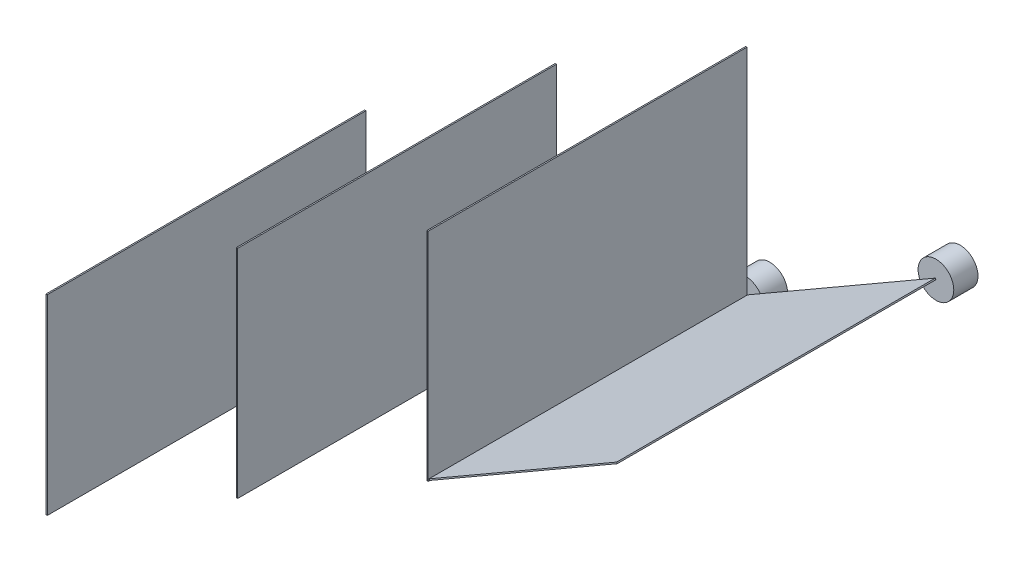
SolidWorks part; units mm, degrees
ref_plane "前视基准面" through (0, 0, 0) normal (0, 0, 1) x (1, 0, 0)
ref_plane "上视基准面" through (0, 0, 0) normal (0, 1, 0) x (1, 0, 0)
ref_plane "右视基准面" through (0, 0, 0) normal (1, 0, 0) x (0, 0, -1)
other "Configuration Table"
sketch "草图1" plane through (0, 0, 0) normal (0, 0, 1) x (1, 0, 0)
  line L0 (0, 0) -> (47.6566, 0) construction
  line L1 (0, 0) -> (147.2243, 85)
  line L2 (0, 0) -> (-0.5, 0.866)
  line L3 (147.2243, 85) -> (146.7243, 85.866)
  line L4 (-0.5, 0.866) -> (146.7243, 85.866)
  line L5 (-2.1651, -1.25) -> (0, 0) construction
  line L6 (-2.1651, -1.25) -> (-151.5544, -87.5) construction
  line L7 (-1.1651, -1.25) -> (-2.1651, -1.25)
  line L8 (-1.1651, -1.25) -> (-1.1651, 168.75)
  line L9 (-1.1651, 168.75) -> (-2.1651, 168.75)
  line L10 (-2.1651, -1.25) -> (-2.1651, 168.75)
  line L11 (-151.5544, -87.5) -> (-300.9438, -173.75) construction
  line L12 (-151.5544, -87.5) -> (-150.5544, -87.5)
  line L13 (-151.5544, -87.5) -> (-151.5544, 82.5)
  line L14 (-151.5544, 82.5) -> (-150.5544, 82.5)
  line L15 (-150.5544, -87.5) -> (-150.5544, 82.5)
  line L17 (-300.9438, -173.75) -> (-299.9438, -173.75)
  line L18 (-300.9438, -173.75) -> (-300.9438, -23.75)
  line L19 (-300.9438, -23.75) -> (-299.9438, -23.75)
  line L20 (-299.9438, -173.75) -> (-299.9438, -23.75)
  dimension "D1" = 30
sketch "草图2" plane through (0, 0, 0) normal (0, 0, 1) x (1, 0, 0)
  circle A0 centre (147.2243, 85) radius 14
  circle A1 centre (-2.1651, -1.25) radius 14
  circle A2 centre (-151.5544, -87.5) radius 14
  circle A3 centre (-300.9438, -173.75) radius 14
extrude "凸台-拉伸2" add sketch "草图1" along normal blind 250
extrude "凸台-拉伸3" add sketch "草图2" against normal blind 19 contours A3 | A2 | A1 | A0
